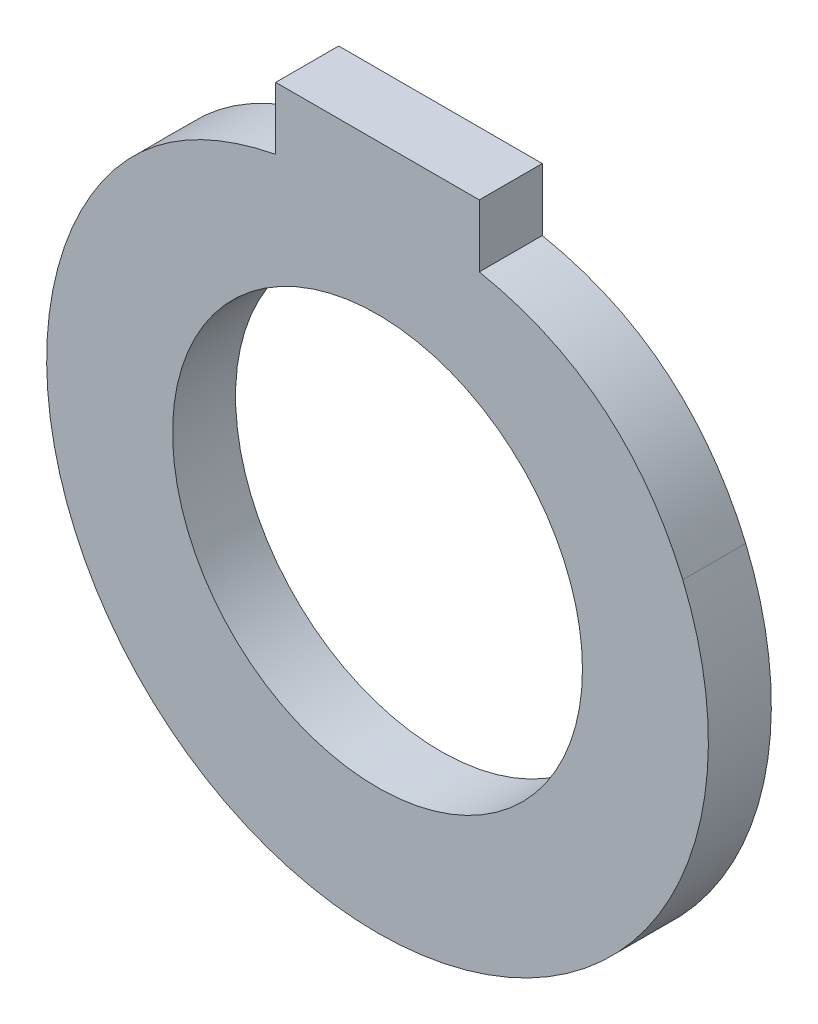
SolidWorks part; units mm, degrees
ref_plane "Front Plane" through (0, 0, 0) normal (0, 0, 1) x (1, 0, 0)
ref_plane "Top Plane" through (0, 0, 0) normal (0, 1, 0) x (1, 0, 0)
ref_plane "Right Plane" through (0, 0, 0) normal (1, 0, 0) x (0, 0, -1)
sketch "Sketch1" plane through (0, 0, 0) normal (0, 0, 1) x (1, 0, 0)
  line L0 (0, 35.7911) -> (0, -20.6693) construction
  line L1 (-30.7878, 35.7911) -> (30.7878, 35.7911) construction
  line L2 (-20.6693, 0) -> (-20.6693, 41.8406) construction
  line L3 (20.6693, 0) -> (20.6693, 41.8406) construction
  line L4 (0, 35.7911) -> (0, 41.8406) construction
  line L5 (-10.2658, 35.7911) -> (10.2658, 35.7911)
  line L8 (-10.2658, 35.7911) -> (-10.2658, 29.5004)
  line L9 (10.2658, 35.7911) -> (10.2658, 29.5004)
  circle A0 centre (0, 0) radius 20.6693
  arc A1 (-30.7878, 12.8692) -> (30.7878, 12.8692) centre (0, 0) ccw
  spline S0 degree 2 poles (-30.7878, 12.8692) (-24.8719, 26.6306) (-10.2658, 29.5004) knots 0 0 0 1 1 1
  spline S1 degree 2 poles (30.7878, 12.8692) (24.8719, 26.6306) (10.2658, 29.5004) knots 0 0 0 1 1 1
extrude "Boss-Extrude1" add sketch "Sketch1" along normal blind 6.35
